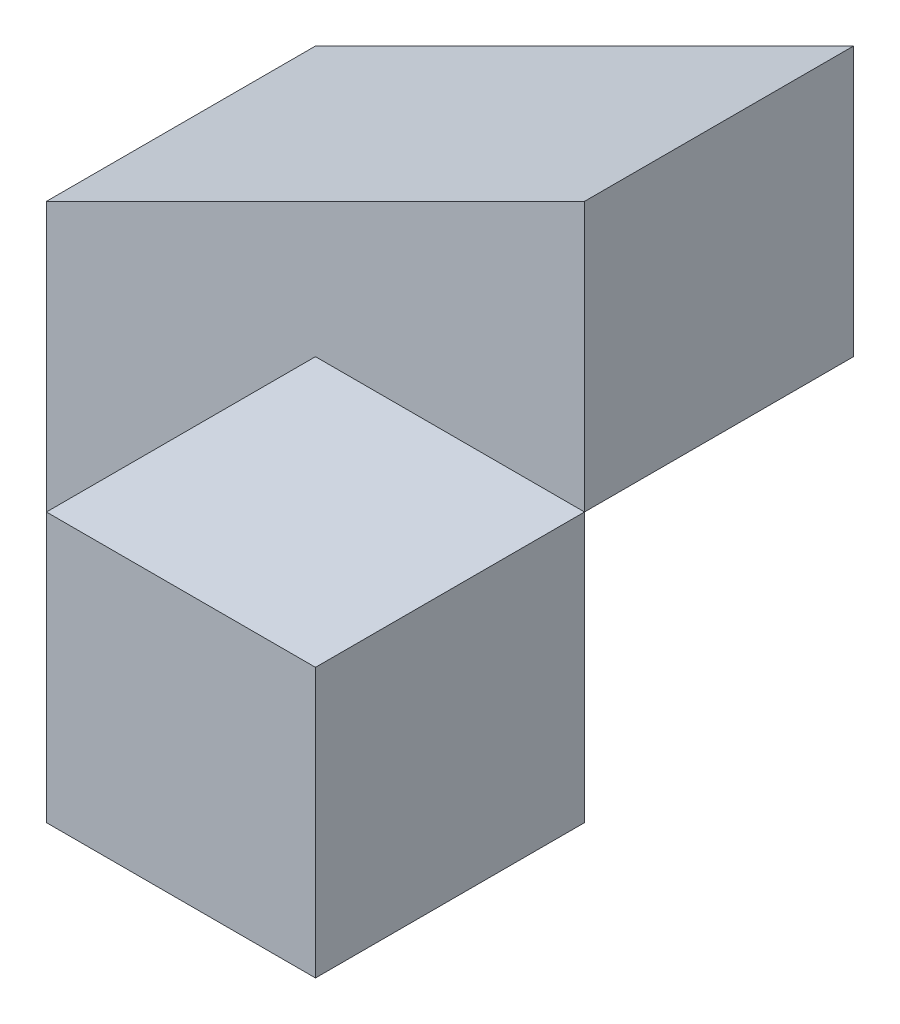
SolidWorks part; units mm, degrees
ref_plane "Front Plane" through (0, 0, 0) normal (0, 0, 1) x (1, 0, 0)
ref_plane "Top Plane" through (0, 0, 0) normal (0, 1, 0) x (1, 0, 0)
ref_plane "Right Plane" through (0, 0, 0) normal (1, 0, 0) x (0, 0, -1)
sketch "Sketch1" plane through (0, 0, 0) normal (0, 0, 1) x (1, 0, 0)
  line L1 (0, 0) -> (40, 0)
  line L2 (0, 0) -> (0, 40)
  line L3 (0, 40) -> (40, 40)
  line L4 (40, 0) -> (40, 40)
  dimension "D1" = 40
  dimension "D2" = 40
extrude "Boss-Extrude1" add sketch "Sketch1" along normal blind 40
sketch "Sketch2" plane through (0, 0, 40) normal (0, 0, 1) x (1, 0, 0)
  line L0 (40, 40) -> (0, 20)
  line L1 (0, 20) -> (0, 40)
  line L2 (0, 40) -> (40, 40)
  dimension "D1" = 20
extrude "Cut-Extrude1" cut sketch "Sketch2" against normal blind 40
sketch "Sketch3" plane through (40, 0, 0) normal (1, 0, 0) x (0, 0, -1)
  line L1 (-40, 40) -> (-20, 40)
  line L2 (-40, 40) -> (-40, 20)
  line L3 (-40, 20) -> (-20, 20)
  line L4 (-20, 40) -> (-20, 20)
  dimension "D1" = 20
  dimension "D2" = 20
extrude "Cut-Extrude2" cut sketch "Sketch3" against normal blind 40
sketch "Sketch4" plane through (0, 0, 0) normal (0, -1, 0) x (1, 0, 0)
  line L0 (40, 20) -> (20, 0)
  line L1 (0, 0) -> (40, 0) construction
  line L2 (20, 0) -> (0, 0)
  line L3 (0, 0) -> (0, 40)
  line L4 (0, 40) -> (40, 40)
  line L5 (40, 40) -> (40, 20)
  line M6 (0, 0) -> (40, 0)
  line M7 (40, 0) -> (40, 40)
extrude "Cut-Extrude3" cut sketch "Sketch4" against normal blind 20 contours L0 M7 M6
sketch "Sketch5" plane through (0, 20, 0) normal (0, 1, 0) x (1, 0, 0)
  line L0 (0, -20) -> (40, -20) construction
  line L1 (20, -20) -> (0, -20)
  line L2 (20, -20) -> (20, -40)
  line L3 (20, -40) -> (0, -40)
  line L4 (0, -20) -> (0, -40)
extrude "Cut-Extrude4" cut sketch "Sketch5" against normal blind 20
